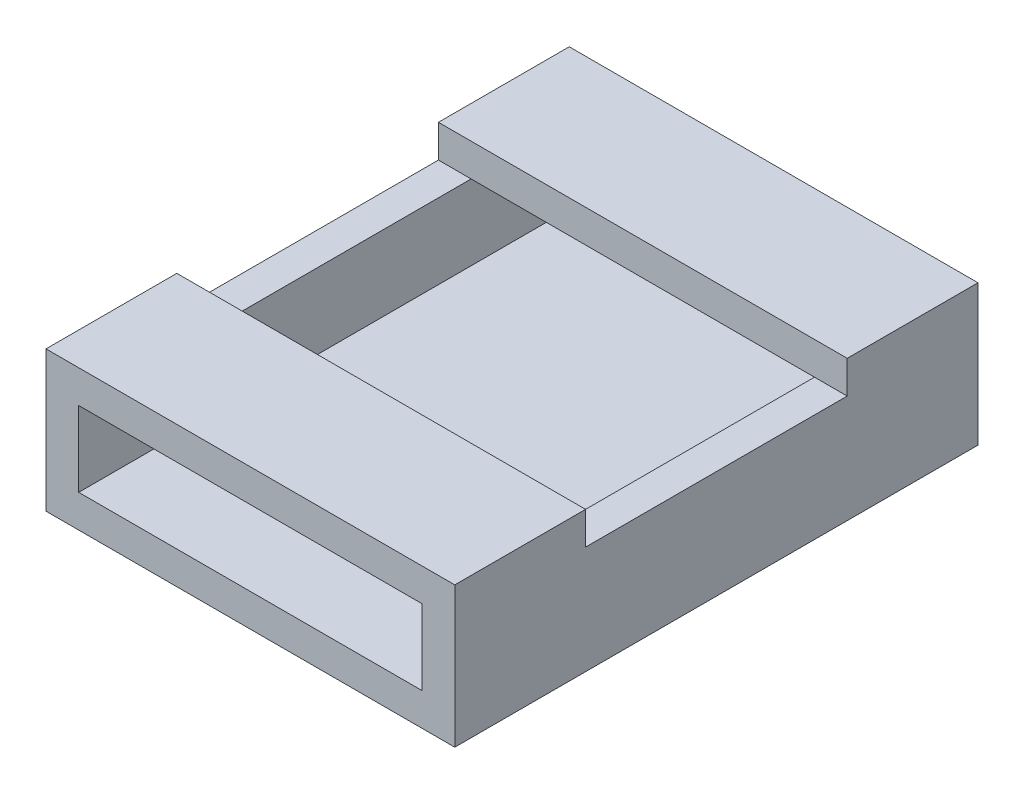
SolidWorks part; units mm, degrees
ref_plane "前视基准面" through (0, 0, 0) normal (0, 0, 1) x (1, 0, 0)
ref_plane "上视基准面" through (0, 0, 0) normal (0, 1, 0) x (1, 0, 0)
ref_plane "右视基准面" through (0, 0, 0) normal (1, 0, 0) x (0, 0, -1)
other "Configuration Table"
sketch "草图1" plane through (0, 0, 0) normal (0, 1, 0) x (1, 0, 0)
  line L1 (0, 0) -> (10.5, 0)
  line L2 (0, 0) -> (0, 4)
  line L3 (0, 4) -> (10.5, 4)
  line L4 (10.5, 0) -> (10.5, 4)
  line L5 (0, 0) -> (10.5, 0)
  line L6 (0, 0) -> (0, -4)
  line L7 (0, -4) -> (10.5, -4)
  line L8 (10.5, 0) -> (10.5, -4)
  line L9 (0, -4) -> (10.5, -4)
  line L10 (0, -4) -> (0, -8)
  line L11 (0, -8) -> (10.5, -8)
  line L12 (10.5, -4) -> (10.5, -8)
  line L13 (0, 4) -> (10.5, 4)
  line L14 (0, 4) -> (0, 8)
  line L15 (0, 8) -> (10.5, 8)
  line L16 (10.5, 4) -> (10.5, 8)
  dimension "D1" = 4
  dimension "D2" = 10.5
  dimension "D3" = 4
  dimension "D4" = 4
  dimension "D5" = 4
sketch "草图2" plane through (0, 0, 0) normal (0, 1, 0) x (1, 0, 0)
  line L1 (0, 8) -> (10.5, 8)
  line L2 (0, 8) -> (0, 4)
  line L3 (0, 4) -> (10.5, 4)
  line L4 (10.5, 8) -> (10.5, 4)
  line L5 (0, 0) -> (10.5, 0)
  line L6 (0, 0) -> (0, 4)
  line L7 (0, 4) -> (10.5, 4)
  line L8 (10.5, 0) -> (10.5, 4)
  line L9 (0, -4) -> (10.5, -4)
  line L10 (0, -4) -> (0, 0)
  line L11 (0, 0) -> (10.5, 0)
  line L12 (10.5, -4) -> (10.5, 0)
  line L13 (0, -8) -> (10.5, -8)
  line L14 (0, -8) -> (0, -4)
  line L15 (0, -4) -> (10.5, -4)
  line L16 (10.5, -8) -> (10.5, -4)
extrude "凸台-拉伸1" add sketch "草图2" along normal blind 1 contours L4 L1 L2 L3 | L5 L8 L3 L6 | L9 L12 L5 L10 | L13 L16 L9 L14
sketch "草图3" plane through (0, 1, 0) normal (0, 1, 0) x (1, 0, 0)
  line L1 (10.5, 8) -> (11.5, 8)
  line L2 (10.5, 8) -> (10.5, -8)
  line L3 (10.5, -8) -> (11.5, -8)
  line L4 (11.5, 8) -> (11.5, -8)
  line L5 (0, 8) -> (-1, 8)
  line L6 (0, 8) -> (0, -8)
  line L7 (0, -8) -> (-1, -8)
  line L8 (-1, 8) -> (-1, -8)
  dimension "D1" = 16
  dimension "D2" = 16
  dimension "D3" = 1
  dimension "D4" = 1
extrude "凸台-拉伸2" add sketch "草图3" along normal blind 2.3 and the other way blind 1
sketch "草图4" plane through (0, 3.3, 0) normal (0, 1, 0) x (1, 0, 0)
  line L0 (11.5, -8) -> (11.5, 8) construction
  line L1 (-1, 8) -> (11.5, 8)
  line L2 (-1, 8) -> (-1, 4)
  line L3 (-1, 4) -> (11.5, 4)
  line L4 (11.5, 8) -> (11.5, 4)
  line L5 (0, -4) -> (10.5, -4) construction
  line L6 (-1, -8) -> (11.5, -8)
  line L7 (-1, -8) -> (-1, -4)
  line L8 (-1, -4) -> (11.5, -4)
  line L9 (11.5, -8) -> (11.5, -4)
  line L10 (0, 4) -> (10.5, 4) construction
extrude "凸台-拉伸3" add sketch "草图4" along normal blind 1
